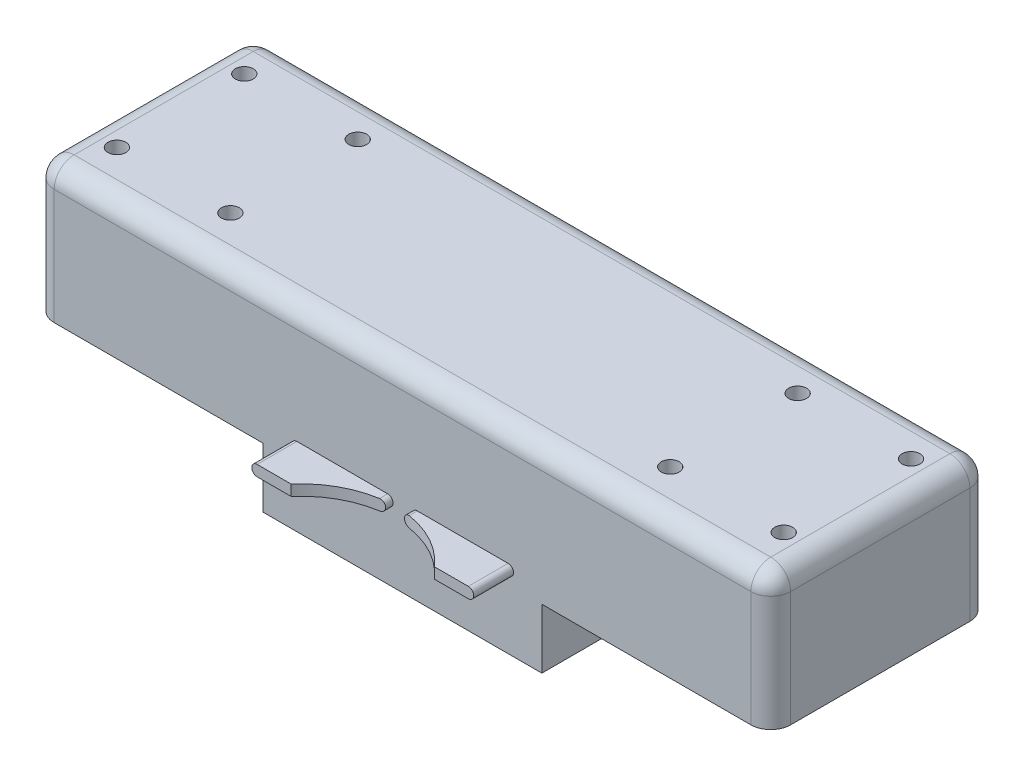
SolidWorks part; units mm, degrees
ref_plane "Front Plane" through (0, 0, 0) normal (0, 0, 1) x (1, 0, 0)
ref_plane "Top Plane" through (0, 0, 0) normal (0, 1, 0) x (1, 0, 0)
ref_plane "Right Plane" through (0, 0, 0) normal (1, 0, 0) x (0, 0, -1)
sketch "Sketch2" plane through (0, 0, 0) normal (0, 0, 1) x (1, 0, 0)
  line L3 (-92.5, 34) -> (92.5, 34)
  line L5 (-92.5, 0) -> (-35, 0)
  line L7 (92.5, 0) -> (35, 0)
  line L8 (-92.5, 0) -> (-92.5, 34)
  line L10 (-35, 0) -> (-35, -15)
  line L11 (-35, -15) -> (35, -15)
  line L12 (35, 0) -> (35, -15)
  line L13 (92.5, 34) -> (92.5, 0)
  point P13 (0, -15)
  dimension "D1" = 185
  dimension "D2" = 34
  dimension "D3" = 15
  dimension "D4" = 70
extrude "Boss-Extrude1" add sketch "Sketch2" along normal blind 55
sketch "Sketch3" plane through (0, 0, 55) normal (0, 0, 1) x (1, 0, 0)
  line L1 (-92.5, 34) -> (92.5, 34)
  line L2 (-92.5, 34) -> (-92.5, -6)
  line L3 (-92.5, -6) -> (92.5, -6)
  line L4 (92.5, 34) -> (92.5, -6)
  point P4 (0, 0)
  dimension "D1" = 40
sketch "Sketch4" plane through (0, 0, 55) normal (0, 0, 1) x (1, 0, 0)
  line L0 (0, 34) -> (0, -6) construction
  line L3 (-3.725, 4.65) -> (-2.375, 4.65) construction
  line L4 (-26.525, 4.65) -> (-3.725, 4.65)
  line L6 (-26.525, 1.95) -> (-3.725, 1.95)
  line L7 (-2.375, 4.65) -> (-2.375, 1.95) construction
  line L8 (-2.375, 1.95) -> (-3.725, 1.95) construction
  line L9 (-26.525, 4.65) -> (-27.875, 4.65) construction
  line L10 (-27.875, 4.65) -> (-27.875, 1.95) construction
  line L11 (-27.875, 1.95) -> (-26.525, 1.95) construction
  line L12 (26.525, 1.95) -> (3.725, 1.95)
  line L13 (26.525, 4.65) -> (3.725, 4.65)
  line L14 (-92.5, 34) -> (92.5, 34) construction
  line L15 (-15.125, 4.65) -> (-15.125, 1.95) construction
  line L16 (-92.5, -6) -> (92.5, -6) construction
  arc A0 (-3.725, 4.65) -> (-3.725, 1.95) centre (-3.725, 3.3) cw
  arc A1 (-26.525, 1.95) -> (-26.525, 4.65) centre (-26.525, 3.3) cw
  arc A2 (3.725, 4.65) -> (3.725, 1.95) centre (3.725, 3.3) ccw
  arc A3 (26.525, 1.95) -> (26.525, 4.65) centre (26.525, 3.3) ccw
  point P2 (0, 0)
  point P3 (0, 21.8798)
  point P4 (0, 0)
  point P5 (0, -12.726)
  point P22 (0, 0)
  point P29 (0, 0)
  point P30 (0, 25)
  point P31 (0, 34)
  dimension "D1" = 25.5
  dimension "D2" = 15.125
  dimension "D3" = 2.7
  dimension "D4" = 30.7
sketch "Sketch6" plane through (0, 0, 0) normal (0, 0, -1) x (-1, 0, 0)
  line L0 (-11.45, 25.475) -> (11.45, 25.475)
  line L1 (0, 34) -> (0, -6) construction
  line L2 (-11.45, 22.875) -> (11.45, 22.875)
  line L3 (0, 55) -> (0, -55) construction
  line L4 (-11.45, 25.475) -> (-12.75, 25.475) construction
  line L5 (-12.75, 25.475) -> (-12.75, 22.875) construction
  line L6 (-12.75, 22.875) -> (-11.45, 22.875) construction
  line L7 (11.45, 25.475) -> (12.75, 25.475) construction
  line L8 (12.75, 25.475) -> (12.75, 22.875) construction
  line L9 (12.75, 22.875) -> (11.45, 22.875) construction
  line L10 (-92.5, 34) -> (92.5, 34) construction
  line L11 (16.8, 25.475) -> (42.2, 25.475)
  line L12 (16.8, 22.875) -> (42.2, 22.875)
  line L13 (16.8, 25.475) -> (15.5, 25.475) construction
  line L14 (15.5, 25.475) -> (15.5, 22.875) construction
  line L15 (15.5, 22.875) -> (16.8, 22.875) construction
  line L16 (42.2, 25.475) -> (43.5, 25.475) construction
  line L17 (43.5, 25.475) -> (43.5, 22.875) construction
  line L18 (43.5, 22.875) -> (42.2, 22.875) construction
  line L19 (-16.8, 22.875) -> (-42.2, 22.875)
  line L20 (-16.8, 25.475) -> (-42.2, 25.475)
  line L21 (-32.2, 7) -> (32.2, 7)
  line L22 (-32.2, 1.4) -> (32.2, 1.4)
  line L23 (0, 34) -> (0, -15) construction
  line L24 (35, -15) -> (-35, -15) construction
  line L25 (32.2, 7) -> (35, 7) construction
  line L26 (35, 7) -> (35, 1.4) construction
  line L27 (35, 1.4) -> (32.2, 1.4) construction
  line L28 (-32.2, 7) -> (-35, 7) construction
  line L29 (-35, 7) -> (-35, -7.5) construction
  line L30 (92.5, 34) -> (-92.5, 34) construction
  line L31 (29.5, 25.475) -> (29.5, 22.875) construction
  arc A0 (-11.45, 25.475) -> (-11.45, 22.875) centre (-11.45, 24.175) ccw
  arc A1 (11.45, 25.475) -> (11.45, 22.875) centre (11.45, 24.175) cw
  arc A2 (16.8, 25.475) -> (16.8, 22.875) centre (16.8, 24.175) ccw
  arc A3 (42.2, 25.475) -> (42.2, 22.875) centre (42.2, 24.175) cw
  arc A4 (-16.8, 25.475) -> (-16.8, 22.875) centre (-16.8, 24.175) cw
  arc A5 (-42.2, 25.475) -> (-42.2, 22.875) centre (-42.2, 24.175) ccw
  arc A6 (-32.2, 7) -> (-32.2, 1.4) centre (-32.2, 4.2) ccw
  arc A7 (32.2, 7) -> (32.2, 1.4) centre (32.2, 4.2) cw
  point P4 (0, 25.475)
  point P37 (0, 7)
  dimension "D8" = 29.8
  dimension "D1" = 2.6
  dimension "D2" = 25.5
  dimension "D3" = 9.825
  dimension "D4" = 28
  dimension "D5" = 9.825
  dimension "D6" = 2.6
  dimension "D7" = 29.5
  dimension "D9" = 70
  dimension "D10" = 5.6
extrude "Boss-Extrude4" add sketch "Sketch4" along normal blind 10
extrude "Boss-Extrude3" add sketch "Sketch6" along normal blind 5
sketch "Sketch7" plane through (0, 0, 0) normal (0, -1, 0) x (1, 0, 0)
  line L0 (-83.75, 45) -> (-77.25, 45)
  line L1 (-83.75, 41) -> (-77.25, 41)
  line L2 (-61.75, 45) -> (-55.25, 45)
  line L3 (-61.75, 41) -> (-55.25, 41)
  line L4 (-55.25, 45) -> (-53.25, 45) construction
  line L5 (-53.25, 45) -> (-53.25, 41) construction
  line L6 (-53.25, 41) -> (-55.25, 41) construction
  line L7 (-83.75, 45) -> (-85.75, 45) construction
  line L8 (-85.75, 45) -> (-85.75, 41) construction
  line L9 (-85.75, 41) -> (-83.75, 41) construction
  line L10 (-77.25, 45) -> (-75.25, 45) construction
  line L11 (-75.25, 45) -> (-75.25, 41) construction
  line L12 (-75.25, 41) -> (-77.25, 41) construction
  line L13 (0, -26.95) -> (0, 26.95) construction
  line L14 (61.75, 45) -> (55.25, 45)
  line L16 (-92.5, 55) -> (-35, 55) construction
  line L17 (61.75, 41) -> (55.25, 41)
  line L18 (83.75, 41) -> (77.25, 41)
  line L19 (83.75, 45) -> (77.25, 45)
  line L31 (-92.5, 27) -> (92.5, 27) construction
  line L32 (-92.5, 55) -> (-92.5, 0) construction
  line L33 (92.5, 55) -> (92.5, 0) construction
  line L34 (-75.25, 13) -> (-77.25, 13) construction
  line L35 (-75.25, 9) -> (-75.25, 13) construction
  line L36 (-77.25, 9) -> (-75.25, 9) construction
  line L37 (-85.75, 13) -> (-83.75, 13) construction
  line L38 (-85.75, 9) -> (-85.75, 13) construction
  line L39 (-83.75, 9) -> (-85.75, 9) construction
  line L40 (-53.25, 13) -> (-55.25, 13) construction
  line L41 (-53.25, 9) -> (-53.25, 13) construction
  line L42 (-55.25, 9) -> (-53.25, 9) construction
  line L43 (83.75, 9) -> (77.25, 9)
  line L44 (83.75, 13) -> (77.25, 13)
  line L45 (61.75, 13) -> (55.25, 13)
  line L46 (61.75, 9) -> (55.25, 9)
  line L47 (-61.75, 13) -> (-55.25, 13)
  line L48 (-61.75, 9) -> (-55.25, 9)
  line L49 (-83.75, 13) -> (-77.25, 13)
  line L50 (-83.75, 9) -> (-77.25, 9)
  arc A0 (-83.75, 41) -> (-83.75, 45) centre (-83.75, 43) cw
  arc A1 (-77.25, 41) -> (-77.25, 45) centre (-77.25, 43) ccw
  arc A2 (-61.75, 41) -> (-61.75, 45) centre (-61.75, 43) cw
  arc A3 (-55.25, 45) -> (-55.25, 41) centre (-55.25, 43) cw
  arc A4 (61.75, 41) -> (61.75, 45) centre (61.75, 43) ccw
  arc A5 (55.25, 45) -> (55.25, 41) centre (55.25, 43) ccw
  arc A6 (83.75, 41) -> (83.75, 45) centre (83.75, 43) ccw
  arc A7 (77.25, 41) -> (77.25, 45) centre (77.25, 43) cw
  arc A8 (77.25, 13) -> (77.25, 9) centre (77.25, 11) ccw
  arc A9 (83.75, 13) -> (83.75, 9) centre (83.75, 11) cw
  arc A10 (55.25, 9) -> (55.25, 13) centre (55.25, 11) cw
  arc A11 (61.75, 13) -> (61.75, 9) centre (61.75, 11) cw
  arc A12 (-55.25, 9) -> (-55.25, 13) centre (-55.25, 11) ccw
  arc A13 (-61.75, 13) -> (-61.75, 9) centre (-61.75, 11) ccw
  arc A14 (-77.25, 13) -> (-77.25, 9) centre (-77.25, 11) cw
  arc A15 (-83.75, 13) -> (-83.75, 9) centre (-83.75, 11) ccw
  point P9 (-83.75, 43)
  point P11 (-55.25, 43)
  point P29 (55.25, 43)
  point P32 (83.75, 43)
  point P107 (83.75, 11)
  point P108 (55.25, 11)
  point P109 (-55.25, 11)
  point P110 (-83.75, 11)
  dimension "D1" = 32.5
  dimension "D2" = 4
  dimension "D3" = 10.5
  dimension "D4" = 139
  dimension "D5" = 10
  dimension "D6" = 14
hole_wizard "CSK for M4 SFHCS2" positions "Sketch7" profile "Sketch9" countersink size "M4" standard "ANSI Metric" end condition through all
sketch "Sketch9" plane through (-83.75, 0, 11) normal (1, 0, 0) x (0, 0, -1)
  line L0 (0, 0) -> (0, 34)
  line L1 (0, 34) -> (2.25, 34)
  line L2 (2.25, 34) -> (2.25, 2.23)
  line L3 (2.25, 2.23) -> (4.48, 0)
  line L5 (4.48, 0) -> (0, 0)
  line L6 (-2.25, 2.23) -> (-4.48, 0) construction
  line L11 (0, -6.35) -> (0, 107.95) construction
  dimension "Thru Hole Dia." = 4.5
  dimension "Thru Hole Depth" = 34
  dimension "Near C'Sink Dia." = 8.96
  dimension "Near C'Sink Angle" = 90
fillet "Fillet4" radius 5 8 edges at (92.5, 17, 0) (92.5, 17, 55) (92.5, 34, 27.5) (0, 34, 0) (-92.5, 17, 0) (-92.5, 34, 27.5) (0, 34, 55) (-92.5, 17, 55)
sketch "Sketch12" plane through (0, 1.95, 0) normal (0, -1, 0) x (1, 0, 0)
  line L1 (-92.5, 55) -> (92.5, 55) construction
  circle A0 centre (0, 80.5) radius 23.75
  point P2 (0, 81.259)
  point P5 (0, 0)
  dimension "D1" = 25.5
extrude "Cut-Extrude2" cut sketch "Sketch12" against normal through all
